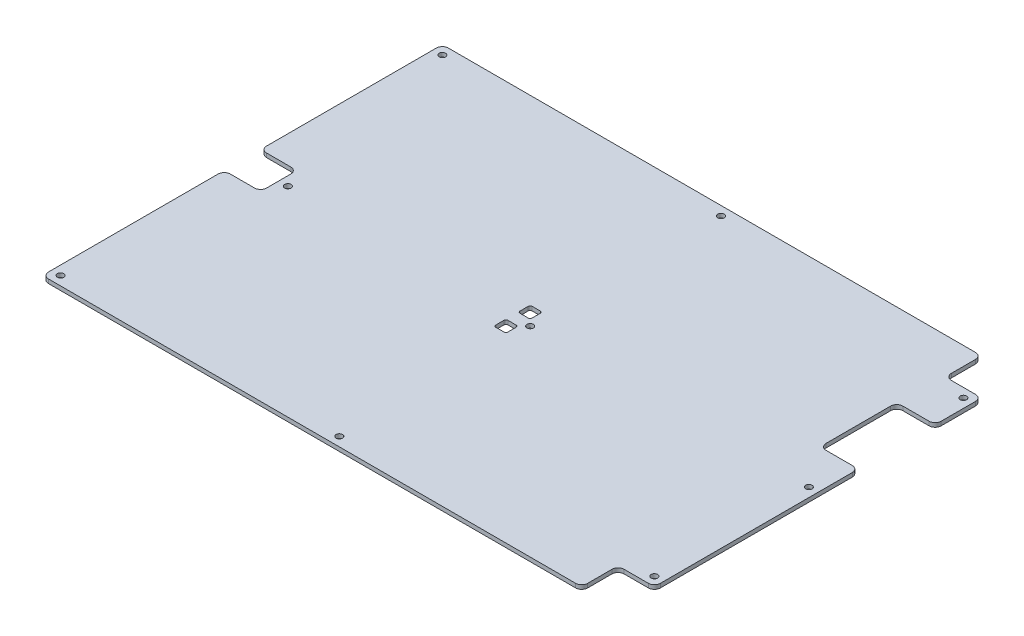
SolidWorks part; units mm, degrees
material "Pino"
ref_plane "Alzado" through (0, 0, 0) normal (0, 0, 1) x (1, 0, 0)
ref_plane "Planta" through (0, 0, 0) normal (0, 1, 0) x (1, 0, 0)
ref_plane "Vista lateral" through (0, 0, 0) normal (1, 0, 0) x (0, 0, -1)
ref_plane "Plano1" through (0, 2, 0) normal (0, 1, 0) x (1, 0, 0)
sketch "Croquis1" plane through (0, 2, 0) normal (0, 1, 0) x (1, 0, 0)
  line L0 (0, 198) -> (0, 108)
  line L1 (0, 0) -> (267, 0)
  line L2 (285, 18) -> (285, 180)
  line L3 (267, 198) -> (0, 198)
  line L4 (285, 99) -> (0, 99) construction
  line L5 (0, 90) -> (0, 0)
  line L6 (0, 108) -> (0, 90) construction
  line L7 (0, 193.5) -> (267, 193.5) construction
  line L13 (0, 108) -> (18, 108)
  line L15 (0, 90) -> (18, 90)
  line L16 (18, 108) -> (18, 90)
  line L17 (267, 198) -> (285, 198) construction
  line L18 (285, 198) -> (285, 180) construction
  line L19 (285, 18) -> (267, 18)
  line L20 (267, 0) -> (267, 18)
  line L21 (267, 0) -> (285, 0) construction
  line L22 (285, 0) -> (285, 18) construction
  line L23 (285, 180) -> (267, 180)
  line L24 (267, 198) -> (267, 180)
  circle A0 centre (69, 193.5) radius 1.6 construction
  circle A1 centre (142.5, 193.5) radius 1.6
  circle A2 centre (4.5, 193.5) radius 1.6
  circle A3 centre (4.5, 112.5) radius 1.6 construction
  circle A4 centre (4.5, 85.5) radius 1.6 construction
  circle A5 centre (280.5, 22.5) radius 1.6
  circle A6 centre (262.5, 4.5) radius 1.6 construction
  circle A7 centre (280.5, 175.5) radius 1.6
  circle A8 centre (280.5, 99) radius 1.6
  circle A9 centre (198, 4.5) radius 1.6 construction
  circle A10 centre (142.5, 4.5) radius 1.6
  circle A11 centre (69, 4.5) radius 1.6 construction
  circle A12 centre (4.5, 4.5) radius 1.6
  circle A13 centre (198, 193.5) radius 1.6 construction
  circle A14 centre (262.5, 193.5) radius 1.6 construction
  circle A15 centre (71, 99) radius 1.6 construction
  circle A16 centre (214, 99) radius 1.6 construction
  circle A17 centre (142.5, 99) radius 1.6
  circle A18 centre (22.5, 99) radius 1.6
  point P35 (0, 99)
  dimension "D13" = 3.2
  dimension "D10" = 71
  dimension "D5" = 4.5
  dimension "D11" = 18
  dimension "D2" = 285
  dimension "D4" = 4.5
  dimension "D6" = 69
  dimension "D7" = 71
  dimension "D8" = 4.5
  dimension "D9" = 4.5
  dimension "D12" = 4.5
  dimension "D18" = 198
  dimension "D19" = 99
  dimension "D22" = 4.5
  dimension "D23" = 4.5
  dimension "D24" = 18
  dimension "D25" = 18
  dimension "D26" = 18
  dimension "D27" = 18
  dimension "D28" = 18
  dimension "D29" = 18
  dimension "D30" = 4.5
  dimension "D36" = 142.5
  dimension "D37" = 198
extrude "Saliente-Extruir1" add sketch "Croquis1" against normal blind 2
fillet "Redondeo1" radius 3 12 edges at (0, 1, -198) (267, 1, -198) (267, 1, -180) (285, 1, -180) (285, 1, -18) (267, 1, -18) (267, 1, 0) (0, 1, 0) (0, 1, -90) (18, 1, -90) (0, 1, -108) (18, 1, -108)
sketch "Croquis2" plane through (0, 2, 0) normal (0, 1, 0) x (1, 0, 0)
  line L0 (285, 21) -> (285, 177) construction
  line L1 (285, 157) -> (275, 157)
  line L2 (285, 157) -> (285, 117)
  line L3 (285, 117) -> (275, 117)
  line L4 (275, 157) -> (275, 117)
  line L5 (282, 180) -> (270, 180) construction
  dimension "D1" = 23
  dimension "D2" = 40
  dimension "D3" = 10
extrude "Cortar-Extruir1" [suppressed] cut sketch "Croquis2" against normal blind 10
fillet "Redondeo2" [suppressed] radius 3
sketch "Croquis3" plane through (0, 2, 0) normal (0, 1, 0) x (1, 0, 0)
  line L1 (285, 157) -> (266, 157)
  line L2 (285, 157) -> (285, 119)
  line L3 (285, 119) -> (266, 119)
  line L4 (266, 157) -> (266, 119)
  line L6 (285, 99) -> (8.6452, 99) construction
  line L7 (285, 21) -> (285, 177) construction
  line L8 (266, 138) -> (285, 138) construction
  dimension "D1" = 39
  dimension "D2" = 38
  dimension "D3" = 19
extrude "Sortida cable llit" cut sketch "Croquis3" against normal through all
fillet "Redondeo3" radius 3 4 edges at (285, 1, -119) (266, 1, -119) (285, 1, -157) (266, 1, -157)
sketch "Croquis4" plane through (0, 0, 0) normal (0, -1, 0) x (1, 0, 0)
  line L0 (133.5, -90) -> (139.5, -96) construction
  line L1 (133.5, -90) -> (139.5, -90)
  line L2 (133.5, -90) -> (133.5, -96)
  line L3 (133.5, -96) -> (139.5, -96)
  line L4 (139.5, -90) -> (139.5, -96)
  line L5 (22.5, -99) -> (280.5, -99) construction
  line L6 (139.5, -108) -> (139.5, -102)
  line L7 (133.5, -102) -> (139.5, -102)
  line L8 (133.5, -108) -> (133.5, -102)
  line L9 (133.5, -108) -> (139.5, -108)
  circle A0 centre (142.5, -99) radius 1.6 construction
  point P4 (136.5, -93)
  point P11 (136.5, -105)
  dimension "D1" = 6
  dimension "D2" = 6
  dimension "D3" = 6
  dimension "D4" = 6
extrude "Forat termistor" cut sketch "Croquis4" against normal through all
fillet "Redondeo4" radius 1 8 edges at (139.5, 1, -96) (133.5, 1, -96) (139.5, 1, -90) (133.5, 1, -90) (133.5, 1, -102) (139.5, 1, -102) (139.5, 1, -108) (133.5, 1, -108)
